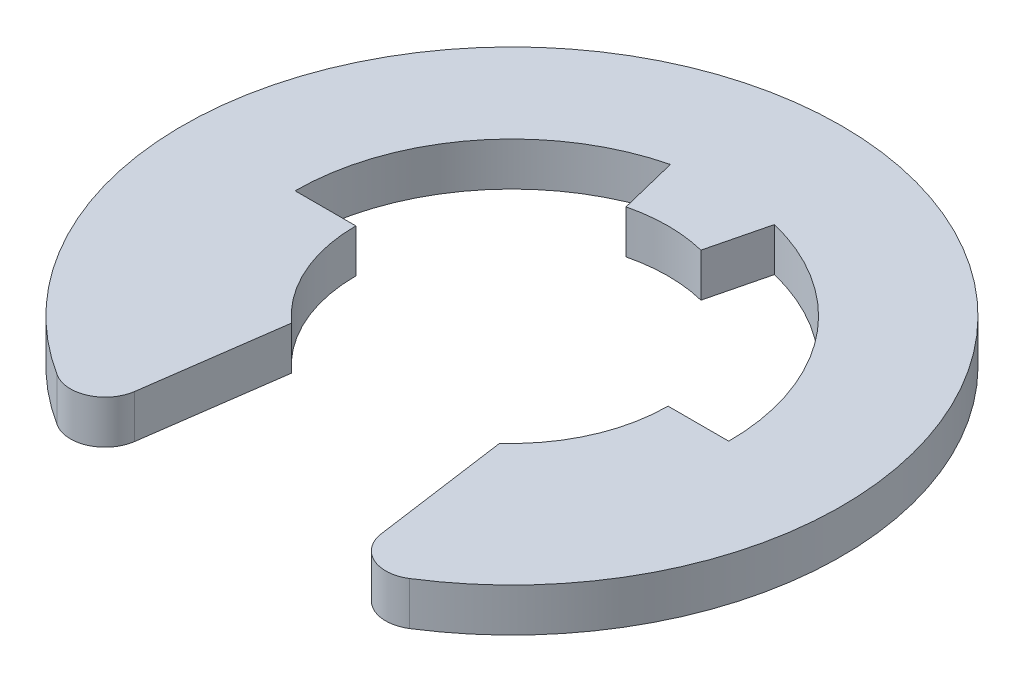
SolidWorks part; units mm, degrees
ref_plane "Front Plane" through (0, 0, 0) normal (0, 0, 1) x (1, 0, 0)
ref_plane "Top Plane" through (0, 0, 0) normal (0, 1, 0) x (1, 0, 0)
ref_plane "Right Plane" through (0, 0, 0) normal (1, 0, 0) x (0, 0, -1)
sketch "Sketch2" plane through (0, 0, 0) normal (0, 1, 0) x (1, 0, 0)
  line L1 (-3.175, 0) -> (-2.286, 0)
  line L2 (0, 0) -> (0, 3.175) construction
  line L3 (0, 0) -> (0.762, 3.0822) construction
  line L9 (0, 0) -> (-0.762, 3.0822) construction
  line L10 (-0.762, 3.0822) -> (-0.5486, 2.2192)
  line L11 (0.762, 3.0822) -> (0.5486, 2.2192)
  line L14 (2.286, 0) -> (3.175, 0)
  line L15 (0, -1000) -> (0, 49000) construction
  line L16 (-1.905, -4.4341) -> (-1.524, -1.7039)
  line L17 (1.905, -4.4341) -> (1.524, -1.7039)
  arc A6 (1.905, -4.4341) -> (-1.905, -4.4341) centre (0, 0) ccw
  arc A7 (3.175, 0) -> (0.762, 3.0822) centre (0, 0) ccw
  arc A8 (1.524, -1.7039) -> (2.286, 0) centre (0, 0) ccw
  arc A9 (-0.762, 3.0822) -> (-3.175, 0) centre (0, 0) ccw
  arc A10 (-2.286, 0) -> (-1.524, -1.7039) centre (0, 0) ccw
  arc A11 (0.5486, 2.2192) -> (-0.5486, 2.2192) centre (0, 0) ccw
  dimension "D1" = 9.652
  dimension "D2" = 6.35
  dimension "D3" = 4.572
  dimension "D4" = 3.81
  dimension "D5" = 1.524
  dimension "D6" = 1.524
extrude "Boss-Extrude1" add sketch "Sketch2" along normal mid plane 0.635
fillet "Fillet1" radius 0.508 2 edges at (1.905, 0, 4.4341) (-1.905, 0, 4.4341)
